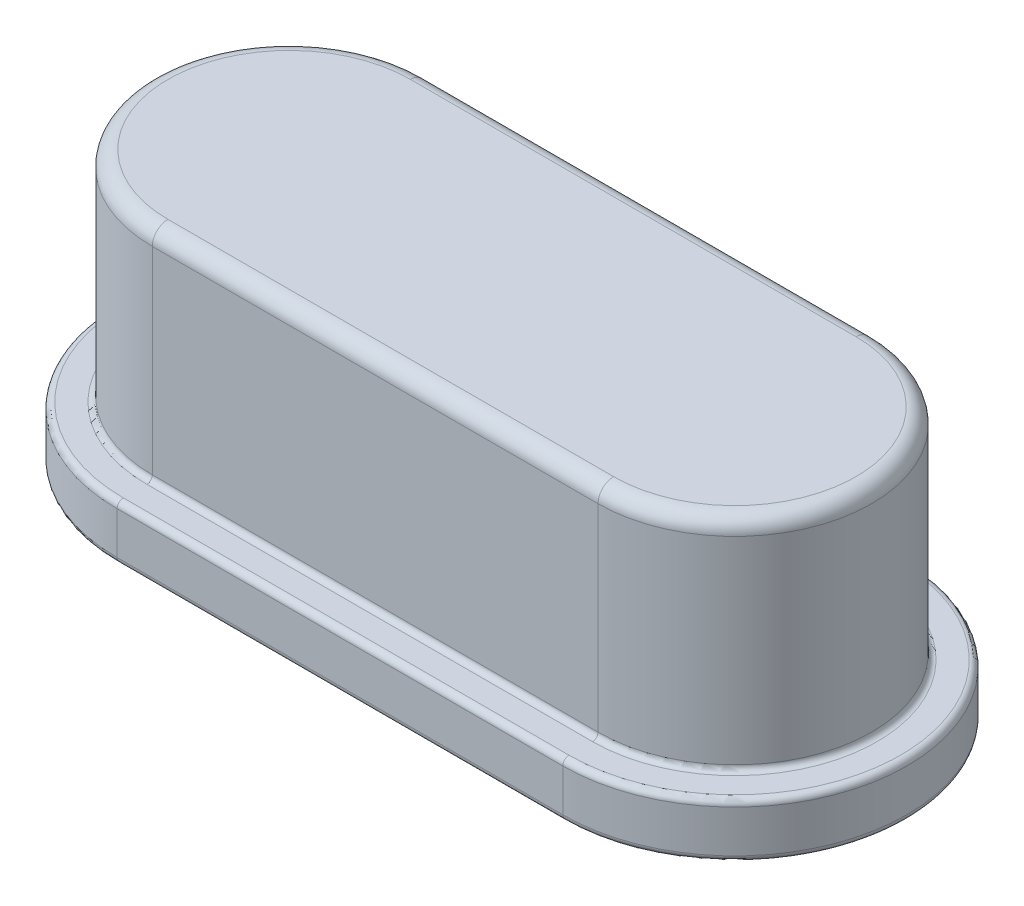
SolidWorks part; units mm, degrees
ref_plane "Front Plane" through (0, 0, 0) normal (0, 0, 1) x (1, 0, 0)
ref_plane "Top Plane" through (0, 0, 0) normal (0, 1, 0) x (1, 0, 0)
ref_plane "Right Plane" through (0, 0, 0) normal (1, 0, 0) x (0, 0, -1)
sketch "Sketch1" plane through (0, 0, 0) normal (0, 1, 0) x (1, 0, 0)
  line L0 (-2.85, 0) -> (2.85, 0) construction
  line L1 (-2.85, 2.2) -> (2.85, 2.2)
  line L2 (-2.85, -2.2) -> (2.85, -2.2)
  arc A0 (-2.85, 2.2) -> (-2.85, -2.2) centre (-2.85, 0) ccw
  arc A1 (2.85, -2.2) -> (2.85, 2.2) centre (2.85, 0) ccw
  point P2 (0, 0)
  point P8 (-5.05, 0)
  point P9 (5.05, 0)
  dimension "D1" = 10.1
  dimension "D2" = 4.4
extrude "Boss-Extrude1" add sketch "Sketch1" along normal blind 0.7
sketch "Sketch2" plane through (0, 0.7, 0) normal (0, 1, 0) x (1, 0, 0)
  line L0 (-2.85, 0) -> (2.85, 0) construction
  line L1 (-2.85, 1.75) -> (2.85, 1.75)
  line L2 (-2.85, -1.75) -> (2.85, -1.75)
  arc A0 (-2.85, 1.75) -> (-2.85, -1.75) centre (-2.85, 0) ccw
  arc A1 (2.85, -1.75) -> (2.85, 1.75) centre (2.85, 0) ccw
  point P2 (0, 0)
  point P8 (-4.6, 0)
  point P9 (4.6, 0)
  dimension "D1" = 3.5
  dimension "D2" = 9.2
extrude "Boss-Extrude2" add sketch "Sketch2" along normal blind 2.8
fillet "Fillet1" radius 0.2 4 edges at (-4.6, 3.5, 0) (0, 3.5, -1.75) (4.6, 3.5, 0) (0, 3.5, 1.75)
fillet "Fillet2" radius 0.08 8 edges at (-5.05, 0, 0) (0, 0, -2.2) (5.05, 0, 0) (-5.05, 0.7, 0) (0, 0.7, -2.2) (5.05, 0.7, 0) (0, 0, 2.2) (0, 0.7, 2.2)
fillet "Fillet3" radius 0.07 4 edges at (-4.6, 0.7, 0) (0, 0.7, -1.75) (4.6, 0.7, 0) (0, 0.7, 1.75)
